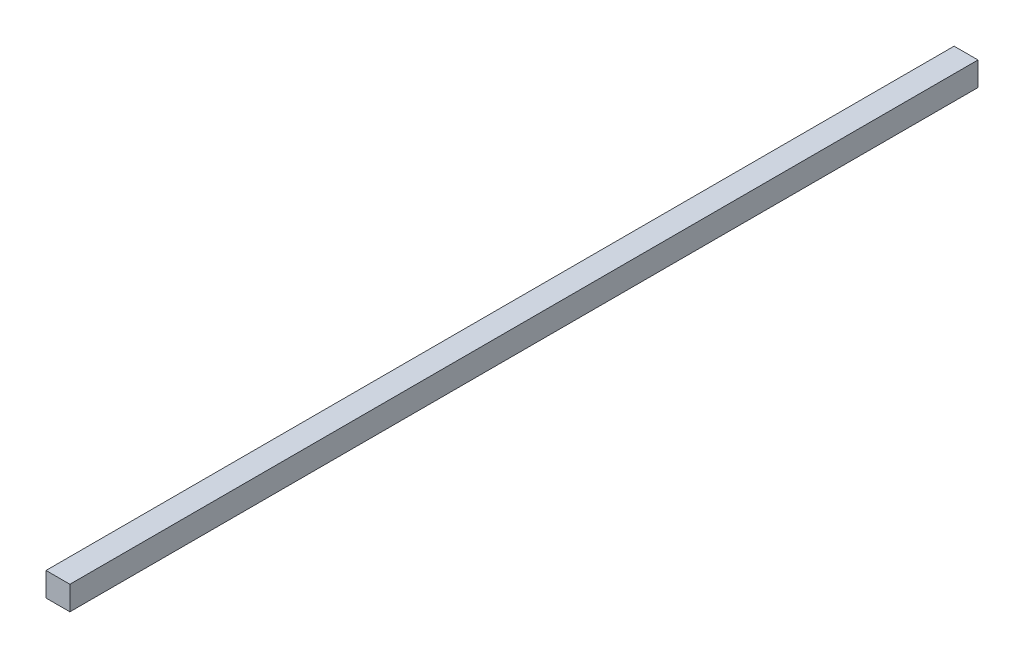
SolidWorks part; units mm, degrees
ref_plane "Front Plane" through (0, 0, 0) normal (0, 0, 1) x (1, 0, 0)
ref_plane "Top Plane" through (0, 0, 0) normal (0, 1, 0) x (1, 0, 0)
ref_plane "Right Plane" through (0, 0, 0) normal (1, 0, 0) x (0, 0, -1)
sketch "Sketch1" plane through (0, 0, 0) normal (0, 0, 1) x (1, 0, 0)
  line L1 (-5, -5) -> (5, -5)
  line L2 (-5, -5) -> (-5, 5)
  line L3 (-5, 5) -> (5, 5)
  line L4 (5, -5) -> (5, 5)
  line L5 (-5, -5) -> (5, 5) construction
  line L6 (-5, 5) -> (5, -5) construction
  point P0 (0, 0)
  dimension "D1" = 10
  dimension "D2" = 10
extrude "Boss-Extrude1" add sketch "Sketch1" against normal blind 380
